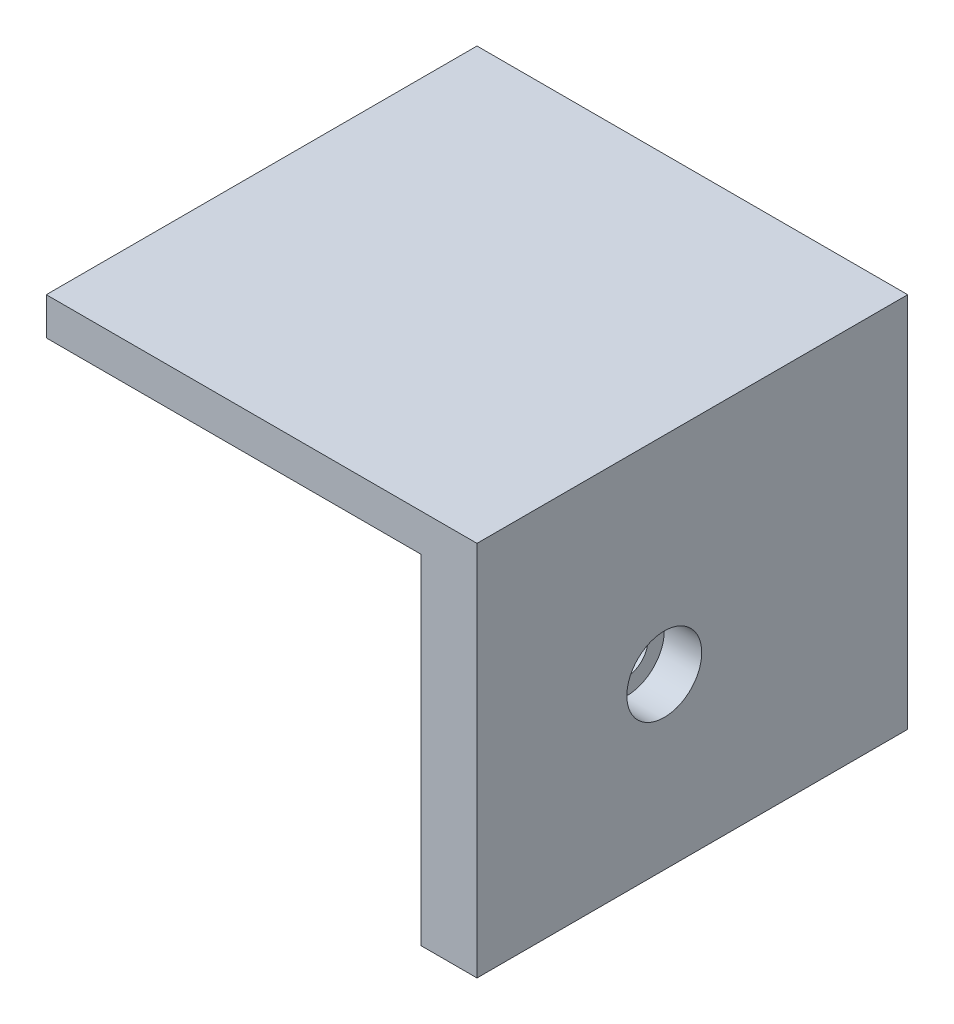
SolidWorks part; units mm, degrees
ref_plane "Front Plane" through (0, 0, 0) normal (0, 0, 1) x (1, 0, 0)
ref_plane "Top Plane" through (0, 0, 0) normal (0, 1, 0) x (1, 0, 0)
ref_plane "Right Plane" through (0, 0, 0) normal (1, 0, 0) x (0, 0, -1)
sketch "Sketch1" plane through (0, 0, 0) normal (0, 1, 0) x (1, 0, 0)
  line L0 (0, 0) -> (0, -40)
  line L1 (0, 0) -> (-40, 0)
  dimension "D1" = 40
extrude "Extrude-Thin1" add sketch "Sketch1" along normal blind 36.2 thin thin type one direction wall 6
sketch "Sketch2" plane through (0, 36.2, 0) normal (0, 1, 0) x (1, 0, 0)
  line L0 (6, -40) -> (0, -40) construction
  line L1 (6, 6) -> (-40, 6)
  line L2 (6, 6) -> (6, -40)
  line L3 (6, -40) -> (-40, -40)
  line L4 (-40, 6) -> (-40, -40)
  line L5 (-40, 0) -> (-40, 6) construction
extrude "Boss-Extrude1" add sketch "Sketch2" along normal blind 4
sketch3d "3DSketch1"
  line L0 (0, 18.1, 40) -> (0, 18.1, 0) construction
  line L1 (0, 36.2, 40) -> (0, 0, 40) construction
  line L2 (0, 36.2, 0) -> (0, 0, 0) construction
  line L3 (0, 18.1, 0) -> (-40, 18.1, 0) construction
  line L4 (-40, 36.2, 0) -> (-40, 0, 0) construction
hole_wizard "CBORE for M4 SHCS1" positions "3DSketch2" profile "Sketch6" counterbore size "M4" standard "ANSI Metric" end condition up to next
sketch3d "3DSketch2"
  line L11 (-40, 18.1, 0) -> (0, 18.1, 0) construction
  line L12 (-40, 36.2, 0) -> (-40, 0, 0) construction
  line L13 (0, 36.2, 0) -> (0, 0, 0) construction
  line L14 (0, 18.1, 0) -> (0, 18.1, 40) construction
  line L15 (0, 36.2, 40) -> (0, 0, 40) construction
  point P0 (6, 18.1, 20)
  point P2 (-20, 18.1, -6)
  point P44 (-20, 18.1, 0)
  point P45 (0, 18.1, 20)
sketch "Sketch6" plane through (6, 18.1, 20) normal (0, 1, 0) x (0, 0, -1)
  line L0 (0, 0) -> (0, 6)
  line L1 (0, 6) -> (2.25, 6)
  line L3 (2.25, 6) -> (2.25, 4)
  line L4 (2.25, 4) -> (4, 4)
  line L5 (4, 4) -> (4, 0)
  line L7 (4, 0) -> (0, 0)
  line L11 (0, -6.35) -> (0, 107.95) construction
  dimension "Thru Hole Dia." = 4.5
  dimension "Thru Hole Depth" = 6
  dimension "C'Bore Dia." = 8
  dimension "C'Bore Depth" = 4
